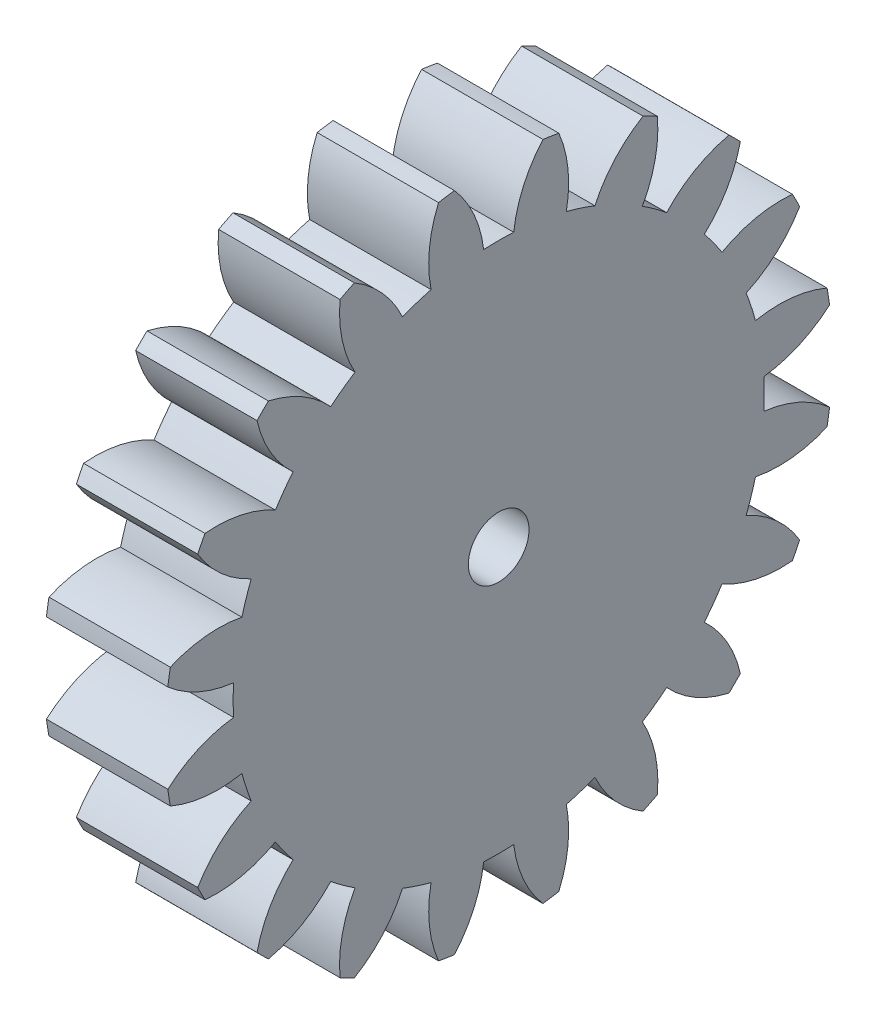
SolidWorks part; units mm, degrees
ref_plane "Plane1" through (0, 0, 0) normal (0, 0, 1) x (1, 0, 0)
ref_plane "Plane2" through (0, 0, 0) normal (0, 1, 0) x (1, 0, 0)
ref_plane "Plane3" through (0, 0, 0) normal (1, 0, 0) x (0, 0, -1)
other "Configuration Table"
sketch "HoldingSke" plane through (0, 0, 0) normal (0, 1, 0) x (1, 0, 0)
  line L0 (0, 0) -> (0.3759, -0.1368)
  line L1 (-15, 0) -> (100, 0) construction
  line L2 (0, 0) -> (-2.1039, 2.3779)
  line L3 (0, 0) -> (-11.863, 4.5341)
  line L4 (0, 0) -> (8.1152, 2.9537)
  line L5 (0, 0) -> (-46.8476, -17.4728)
  line L6 (0, 0) -> (-8.2896, -5.593)
  line L7 (-2.1039, 2.3779) -> (8.6586, 51.2059)
  line L8 (-76.2, 54.61) -> (-75.3, 54.61)
  line L9 (-71.009, 38.7566) -> (-53.1078, 45.2721)
  line L10 (-76.2, 71.12) -> (104.1128, 71.12)
  line L11 (0, 0) -> (-10, 0)
  line L12 (-76.2, 101.6) -> (-76.113, 101.6)
  line L13 (24.9733, 27.94) -> (52.9518, 28.4284)
  line L14 (24.9733, 27.94) -> (24.9743, 27.94)
  line L15 (24.9733, 27.94) -> (100.4006, 29.5858)
  line L16 (-63.627, -2.5) -> (-12.827, -2.5)
  circle A0 centre (0, 0) radius 2.5
  circle A1 centre (0, 0) radius 21.874
  circle A2 centre (0, 0) radius 37.5
  circle A3 centre (0, 0) radius 2.5
  dimension "Hub_dia" = 75
  dimension "Pitch" = 0.4
  dimension "Overall_len" = 50
  dimension "OAL" = 50.0001
  dimension "Ap" = 20
  dimension "H" = 19.05
  dimension "Pitch_radius" = 180.3128
  dimension "Backlash" = 0.087
  dimension "Addendum_fac" = 1
  dimension "Dedendum_fac" = 1.25
  dimension "Clearance_fac" = 0.25
  dimension "Dedendum_add" = 0.001
  dimension "Module" = 2.5
sketch "BasProSke" plane through (0, 0, 0) normal (0, 1, 0) x (1, 0, 0)
  line L0 (-10, 0) -> (60, 0) construction
  line L1 (0, 0) -> (0, 27.5)
  line L2 (0, 0) -> (10, 0)
  line L3 (10, 0) -> (10, 27.5)
  line L4 (10, 27.5) -> (0, 27.5)
revolve "Base-Revolve" add sketch "BasProSke" angle 360 about L0
sketch "TooCutSke" plane through (0, 0, 0) normal (1, 0, 0) x (0, 0, -1)
  line L1 (0, 0) -> (0, 107) construction
  line L2 (0, 0) -> (-2.1137, 24.9105) construction
  line L3 (0, 0) -> (-7.8012, 49.2549) construction
  line L4 (-2.1137, 24.9105) -> (-3.9006, 24.6275) construction
  arc A0 (1.2377, 21.839) -> (-1.2377, 21.839) centre (0, 0) ccw
  arc A1 (3.6672, 27.28) -> (-3.6672, 27.28) centre (0, 0) ccw
  circle A2 centre (0, 0) radius 25 construction
  circle A3 centre (0, 0) radius 23.4923 construction
  arc A4 (-1.2377, 21.839) -> (-3.6672, 27.28) centre (-11.1689, 20.6675) ccw
  arc A5 (3.6672, 27.28) -> (1.2377, 21.839) centre (11.1689, 20.6675) ccw
  dimension "Half_CT" = 1.8092
extrude "ToothCut" cut sketch "TooCutSke" along normal through all
fillet "Breaks" [suppressed] radius 0.05
fillet "RootFillets" [suppressed] radius 0.626
pattern_circular "TeethCuts" count 20 every 18 about axis through (-10, 0, 0) along (1, 0, 0) of "ToothCut", "RootFillets", "Breaks"
sketch "HubNeaOneSke" plane through (0, 0, 0) normal (-1, 0, 0) x (0, 0, 1)
  circle A0 centre (0, 0) radius 21.874
extrude "HubNearOne" [suppressed] add sketch "HubNeaOneSke" along normal blind 40.0001
sketch "HubNeaBotSke" plane through (0, 0, 0) normal (-1, 0, 0) x (0, 0, 1)
  circle A0 centre (0, 0) radius 21.874
extrude "HubNearBoth" [suppressed] add sketch "HubNeaBotSke" along normal blind 20
ref_plane "FarPln" through (10, 0, 0) normal (1, 0, 0) x (0, 0, -1)
sketch "HubFarSke" plane through (10, 0, 0) normal (1, 0, 0) x (0, 0, -1)
  circle A0 centre (0, 0) radius 21.874
extrude "HubFar" [suppressed] add sketch "HubFarSke" along normal blind 20
sketch "BorSke" plane through (0, 0, 0) normal (1, 0, 0) x (0, 0, -1)
  circle A0 centre (0, 0) radius 2.5
extrude "Bore" cut sketch "BorSke" along normal mid plane 100.0001
sketch "KeySke" plane through (0, 0, 0) normal (1, 0, 0) x (0, 0, -1)
  line L0 (-1, 0) -> (-1, 3.4)
  line L1 (-1, 3.4) -> (1, 3.4)
  line L2 (1, 3.4) -> (1, 0)
  line L3 (0, 0) -> (0, 34) construction
  line L4 (-1, 0) -> (1, 0)
  dimension "Width" = 2
extrude "Keyway" [suppressed] cut sketch "KeySke" along normal mid plane 100.0001
pattern_circular "Keyway2" [suppressed] count 2 every 90 about axis through (-10, 0, 0) along (1, 0, 0)
equation "' \"Module@HoldingSke\" = 6.35"
equation "' \"Num_teeth@HoldingSke\" = 12"
equation "' \"Ap@HoldingSke\" =  20"
equation "' \"Ap@HoldingSke\" = 20"
equation "' \"Width@HoldingSke\" = 0.5 * 25.4"
equation "' \"Hub_dia@HoldingSke\"= 1 * 25.4"
equation "' \"Hub_dia@HoldingSke\" = 1 * 25.4"
equation "' \"Overall_len@HoldingSke\" = 1.0 * 25.4"
equation "' \"Bore@HoldingSke\" = 0.75 * 25.4"
equation "' \"T_dim@HoldingSke\" = 0.1 * 25.4"
equation "' \"Width@KeySke\" = 0.25 * 25.4"
equation "' \"Show_teeth@HoldingSke\" = 13"
equation "' \"Backlash@HoldingSke\" = 0.009 * 25.4"
equation "' \"Addendum_fac@HoldingSke\" = 1.0"
equation "' \"Dedendum_fac@HoldingSke\" = 1.25"
equation "' \"Dedendum_add@HoldingSke\" = 0.00005 * 25.4"
equation "' \"Clearance_fac@HoldingSke\" = 0.25"
equation "\"Pitch@HoldingSke\" = 1 / \"Module@HoldingSke\""
equation "\"Overcut_dia@TooCutSke\" = (\"Num_teeth@HoldingSke\" + 2 * \"Addendum_fac@HoldingSke\") / \"Pitch@HoldingSke\" + 0.002 * 25.4"
equation "\"Pitch_dia@TooCutSke\" = \"Num_teeth@HoldingSke\" / \"Pitch@HoldingSke\""
equation "\"Base_dia@TooCutSke\" = \"Num_teeth@HoldingSke\" / \"Pitch@HoldingSke\" * cos((\"Ap@HoldingSke\"  * 3.14159265 / 180))"
equation "\"Root_dia@TooCutSke\" = (\"Num_teeth@HoldingSke\" + 2) / \"Pitch@HoldingSke\" - 2 * (\"Addendum_fac@HoldingSke\" + \"Dedendum_fac@HoldingSke\") / \"Pitch@HoldingSke\" - \"Dedendum_add@HoldingSke\" * 2"
equation "\"Half_ang@TooCutSke\" = 180 / \"Num_teeth@HoldingSke\""
equation "\"Half_CT@TooCutSke\" = \"Num_teeth@HoldingSke\" / \"Pitch@HoldingSke\" * sin((3.14159265 / 2 / \"Num_teeth@HoldingSke\")) / 2 - 7 * \"Backlash@HoldingSke\" / 4"
equation "\"Flank_rad@TooCutSke\" = \"Num_teeth@HoldingSke\" / \"Pitch@HoldingSke\" / 5"
equation "\"Radius@RootFillets\" = \"Clearance_fac@HoldingSke\" / \"Pitch@HoldingSke\" + \"Dedendum_add@HoldingSke\""
equation "\"Break_rad@Breaks\" = 0.02 / \"Pitch@HoldingSke\""
equation "\"Thickness@HoldingSke\" = \"Width@HoldingSke\""
equation "\"OAL@HoldingSke\" = \"Thickness@HoldingSke\""
equation "\"MHD@HoldingSke\" = (\"Num_teeth@HoldingSke\" + 2) / \"Pitch@HoldingSke\" - 2 * (\"Addendum_fac@HoldingSke\" + \"Dedendum_fac@HoldingSke\")  / \"Pitch@HoldingSke\" - \"Dedendum_add@HoldingSke\" * 2"
equation "\"MBD@HoldingSke\" = (\"Num_teeth@HoldingSke\" + 2) / \"Pitch@HoldingSke\" - 2 * (\"Addendum_fac@HoldingSke\" + \"Dedendum_fac@HoldingSke\")  / \"Pitch@HoldingSke\" - \"Dedendum_add@HoldingSke\" * 2 - 0.002 * 25.4"
equation "\"MHD@HoldingSke\" = ((sgn( \"MHD@HoldingSke\" - \"Hub_dia@HoldingSke\" )-1)*( \"MHD@HoldingSke\" - \"Hub_dia@HoldingSke\" ))/-2+ \"Hub_dia@HoldingSke\""
equation "\"MBD@HoldingSke\" = ((sgn( \"MBD@HoldingSke\" - \"Bore@HoldingSke\" )-1)*( \"MBD@HoldingSke\" - \"Bore@HoldingSke\" ))/-2+ \"Bore@HoldingSke\""
equation "\"OAL@HoldingSke\" = ((sgn( \"OAL@HoldingSke\" - \"Overall_len@HoldingSke\" )+1)*( \"OAL@HoldingSke\" - \"Overall_len@HoldingSke\" ))/2 + \"Overall_len@HoldingSke\" + 0.000002 * 25.4"
equation "\"Num_teeth@TeethCuts\" = int( \"Show_teeth@HoldingSke\" ) + 1"
equation "\"Num_teeth@TeethCuts\" = ((sgn( \"Num_teeth@TeethCuts\" - \"Num_teeth@HoldingSke\" )-1)*( \"Num_teeth@TeethCuts\" - \"Num_teeth@HoldingSke\" ))/-2+ \"Num_teeth@HoldingSke\""
equation "\"Num_teeth@TeethCuts\" = ((sgn( \"Num_teeth@TeethCuts\" - 2.0)+1)*( \"Num_teeth@TeethCuts\" - 2.0))/2 +2.0"
equation "\"Angle@TeethCuts\" = 360.0 / \"Num_teeth@HoldingSke\""
equation "\"Diameter@BasProSke\" = (\"Num_teeth@HoldingSke\" + 2 * \"Addendum_fac@HoldingSke\") / \"Pitch@HoldingSke\""
equation "\"Thickness@BasProSke\"  = \"Thickness@HoldingSke\""
equation "' \"Fillet_rad@BasProSke\" =  \"Thickness@HoldingSke\" * 0.05"
equation "' \"Fillet_rad@BasProSke\" = \"Thickness@HoldingSke\" * 0.05"
equation "\"MHD@HoldingSke\" = ((sgn( \"MHD@HoldingSke\" - \"Root_dia@TooCutSke\" )-1)*( \"MHD@HoldingSke\" - \"Root_dia@TooCutSke\" ))/-2+ \"Root_dia@TooCutSke\""
equation "\"Diameter@HubNeaOneSke\" = \"MHD@HoldingSke\""
equation "\"Length@HubNearOne\" = \"OAL@HoldingSke\" - \"Thickness@BasProSke\""
equation "\"Diameter@HubNeaBotSke\" = \"MHD@HoldingSke\""
equation "\"Length@HubNearBoth\" = ( \"OAL@HoldingSke\" - \"Thickness@BasProSke\" ) / 2.0"
equation "\"Thickness@FarPln\" = \"Thickness@BasProSke\""
equation "\"Diameter@HubFarSke\" = \"MHD@HoldingSke\""
equation "\"Length@HubFar\" = ( \"OAL@HoldingSke\" - \"Thickness@BasProSke\" ) / 2.0"
equation "\"Diameter@BorSke\" = \"MBD@HoldingSke\""
equation "\"D1@Bore\" = \"OAL@HoldingSke\" * 2.0"
equation "\"D1@Keyway\" = \"OAL@HoldingSke\" * 2.0"
equation "\"Offset@KeySke\" = \"T_dim@HoldingSke\" + \"MBD@HoldingSke\" / 2.0"
